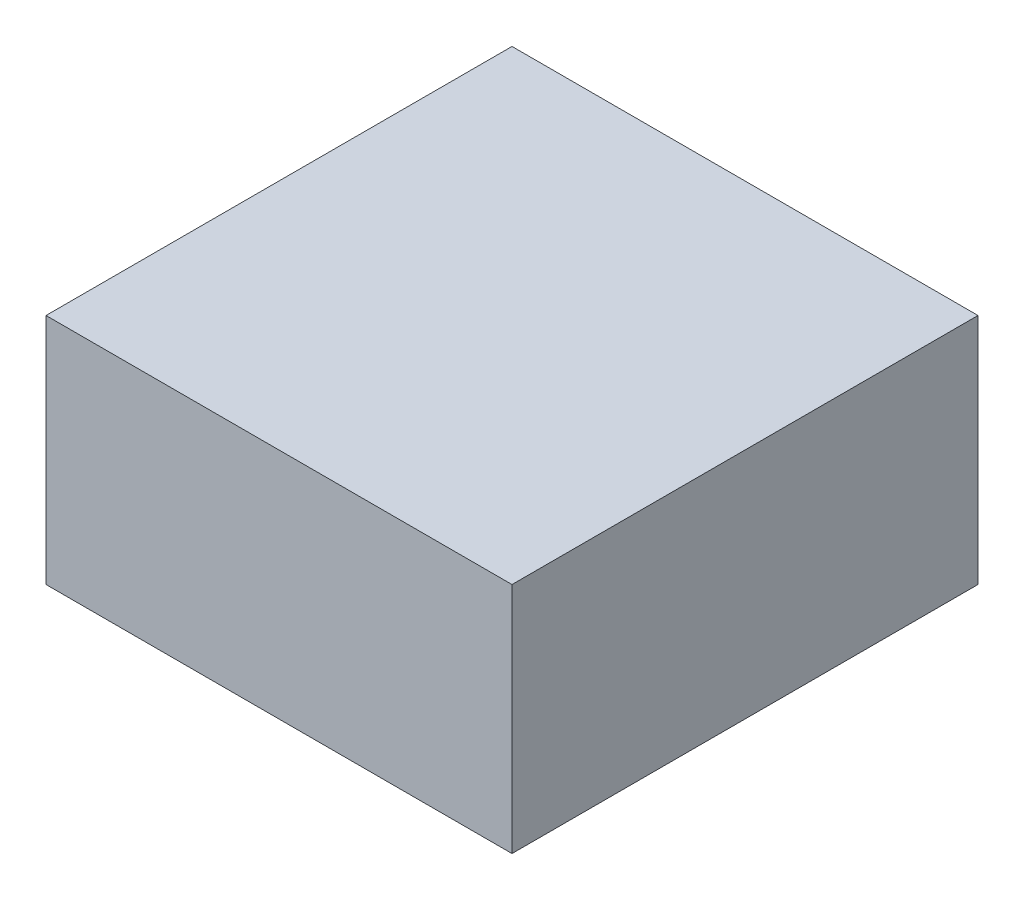
SolidWorks part; units mm, degrees
ref_plane "Front Plane" through (0, 0, 0) normal (0, 0, 1) x (1, 0, 0)
ref_plane "Top Plane" through (0, 0, 0) normal (0, 1, 0) x (1, 0, 0)
ref_plane "Right Plane" through (0, 0, 0) normal (1, 0, 0) x (0, 0, -1)
sketch "Sketch1" plane through (0, 0, 0) normal (0, 1, 0) x (1, 0, 0)
  line L1 (-250, -250) -> (250, -250)
  line L2 (-250, -250) -> (-250, 250)
  line L3 (-250, 250) -> (250, 250)
  line L4 (250, -250) -> (250, 250)
  line L5 (-250, -250) -> (250, 250) construction
  line L6 (-250, 250) -> (250, -250) construction
  point P0 (0, 0)
  dimension "D1" = 500
  dimension "D2" = 500
extrude "Extrude1" add sketch "Sketch1" along normal mid plane 250
